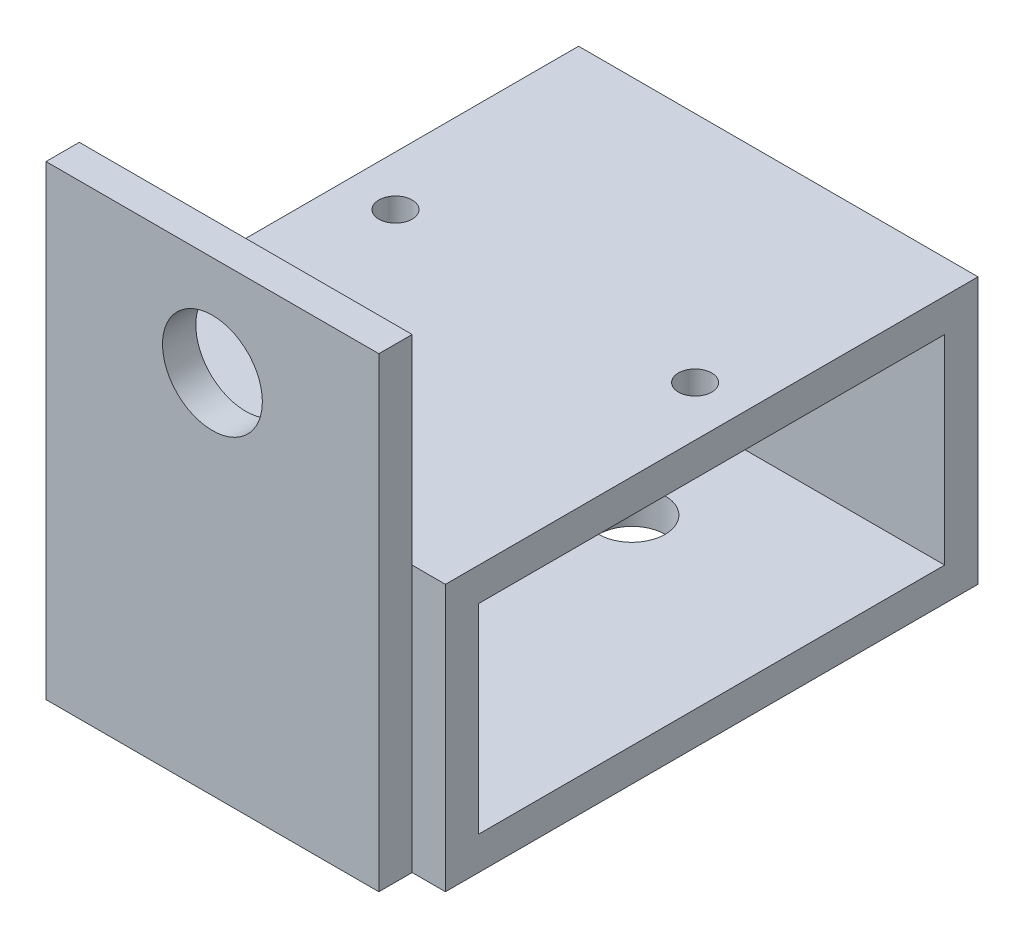
SolidWorks part; units mm, degrees
ref_plane "Front Plane" through (0, 0, 0) normal (0, 0, 1) x (1, 0, 0)
ref_plane "Top Plane" through (0, 0, 0) normal (0, 1, 0) x (1, 0, 0)
ref_plane "Right Plane" through (0, 0, 0) normal (1, 0, 0) x (0, 0, -1)
sketch "Sketch1" plane through (0, 0, 0) normal (1, 0, 0) x (0, 0, -1)
  line L1 (-25.4, -12.7) -> (25.4, -12.7)
  line L2 (-25.4, -12.7) -> (-25.4, 12.7)
  line L3 (-25.4, 12.7) -> (25.4, 12.7)
  line L4 (25.4, -12.7) -> (25.4, 12.7)
  line L5 (-25.4, -12.7) -> (25.4, 12.7) construction
  line L6 (-25.4, 12.7) -> (25.4, -12.7) construction
  point P0 (0, 0)
  dimension "D1" = 25.4
  dimension "D2" = 50.8
extrude "Extrude-Thin1" add sketch "Sketch1" along normal mid plane 38.1 thin thin type one direction reverse wall 3.175
sketch "Sketch2" plane through (0, -12.7, 0) normal (0, -1, 0) x (1, 0, 0)
  line L0 (-15.875, 25.4) -> (-15.875, 28.575)
  line L1 (-15.875, 28.575) -> (15.875, 28.575)
  line L2 (15.875, 28.575) -> (15.875, 25.4)
  line L3 (-19.05, 25.4) -> (19.05, 25.4)
  line L7 (-19.05, 25.4) -> (-19.05, -25.4)
  line L8 (-19.05, -25.4) -> (19.05, -25.4)
  line L9 (19.05, -25.4) -> (19.05, 25.4)
  line L10 (19.05, 25.4) -> (-19.05, 25.4)
  line L11 (-19.05, 25.4) -> (-19.05, -25.4)
  line L12 (-19.05, -25.4) -> (19.05, -25.4)
  line L13 (19.05, -25.4) -> (19.05, 25.4)
  dimension "D1" = 3.175
  dimension "D3" = 3.175
  dimension "D4" = 3.175
  dimension "D2" = 0
extrude "Boss-Extrude1" add sketch "Sketch2" against normal blind 44.45
sketch "Sketch3" plane through (0, 0, 28.575) normal (0, 0, 1) x (1, 0, 0)
  line L1 (0, -12.7) -> (0, 22.225) construction
  line L2 (-15.875, -12.7) -> (15.875, -12.7) construction
  circle A0 centre (0, 22.225) radius 4.7625
  point P0 (0, -12.7)
  dimension "D2" = 9.525
  dimension "D1" = 34.925
extrude "Cut-Extrude1" cut sketch "Sketch3" against normal up to surface (3.175 mm away)
sketch "Sketch4" plane through (0, 12.7, 0) normal (0, 1, 0) x (1, 0, 0)
  line L1 (14.2875, 3.175) -> (-14.2875, 3.175) construction
  line L2 (19.05, 25.4) -> (-19.05, 25.4) construction
  circle A0 centre (14.2875, 3.175) radius 1.5875
  circle A1 centre (-14.2875, 3.175) radius 1.5875
  point P4 (0, 3.175)
  point P5 (0, 25.4)
  dimension "D2" = 3.175
  dimension "D3" = 3.175
  dimension "D1" = 28.575
  dimension "D4" = 22.225
extrude "Cut-Extrude2" cut sketch "Sketch4" against normal up to next
sketch "Sketch7" plane through (0, 12.7, 0) normal (0, 1, 0) x (1, 0, 0)
  line L0 (15.875, -25.4) -> (-15.875, -25.4) construction
  line L1 (12.7, -19.05) -> (-12.7, -19.05)
  line L2 (12.7, -19.05) -> (12.7, 6.35)
  line L3 (12.7, 6.35) -> (-12.7, 6.35)
  line L4 (-12.7, -19.05) -> (-12.7, 6.35)
  line L5 (19.05, 25.4) -> (-19.05, 25.4) construction
  line L6 (19.05, 25.4) -> (19.05, -25.4) construction
  line L7 (-19.05, 25.4) -> (-19.05, -25.4) construction
  dimension "D1" = 6.35
  dimension "D2" = 19.05
  dimension "D3" = 6.35
  dimension "D4" = 6.35
extrude "Cut-Extrude3" [suppressed] cut sketch "Sketch7" against normal up to surface (3.175 mm away)
sketch "Sketch8" plane through (0, -12.7, 0) normal (0, -1, 0) x (1, 0, 0)
  line L1 (19.05, -25.4) -> (-19.05, -25.4) construction
  line L2 (0, 28.575) -> (0, -25.4) construction
  line L3 (-15.875, 28.575) -> (15.875, 28.575) construction
  circle A0 centre (0, -11.43) radius 3.175
  circle A1 centre (0, 11.43) radius 3.175
  point P6 (0, -25.4)
  dimension "D2" = 6.35
  dimension "D3" = 6.35
  dimension "D1" = 17.145
  dimension "D5" = 13.97
extrude "Cut-Extrude4" cut sketch "Sketch8" against normal up to surface (3.175 mm away) up to face at (0, -9.525, 0)
